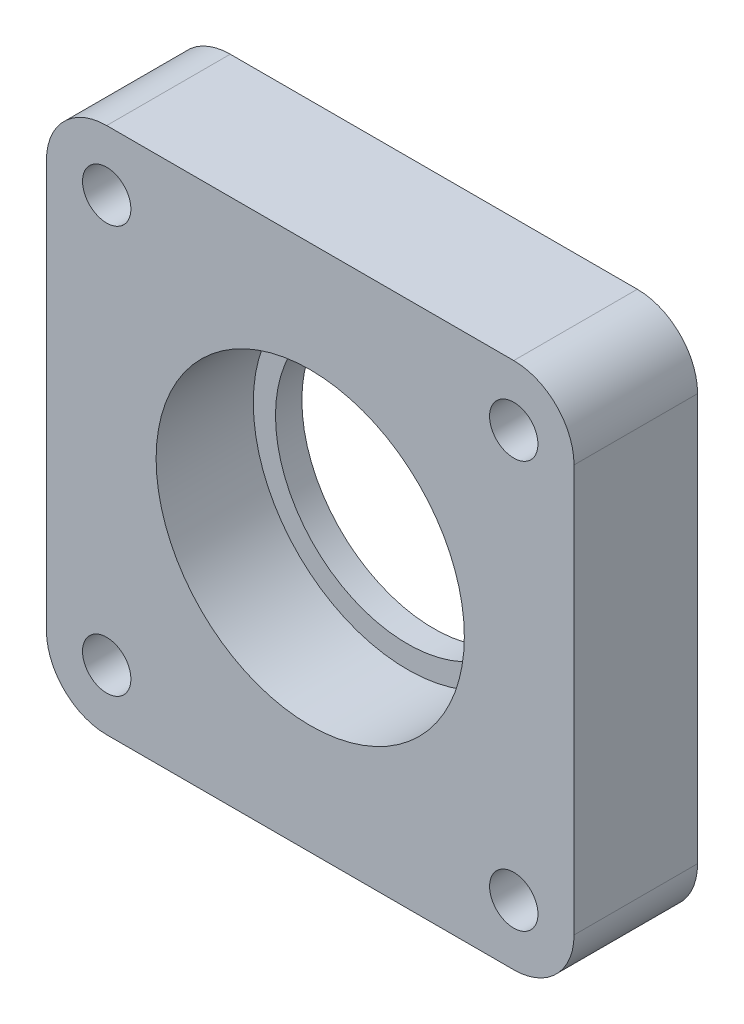
SolidWorks part; units mm, degrees
ref_plane "Alzado" through (0, 0, 0) normal (0, 0, 1) x (1, 0, 0)
ref_plane "Planta" through (0, 0, 0) normal (0, 1, 0) x (1, 0, 0)
ref_plane "Vista lateral" through (0, 0, 0) normal (1, 0, 0) x (0, 0, -1)
sketch "Croquis1" plane through (0, 0, 0) normal (0, 0, 1) x (1, 0, 0)
  line L0 (-122.1468, 83.6784) -> (-122.1468, -52.8591) construction
  line L5 (-172.2499, 0.9592) -> (-2.4287, 0.9592) construction
  line L7 (-99.0018, 30.9592) -> (-145.2918, 30.9592)
  line L8 (-92.1468, 24.1042) -> (-92.1468, -22.1858)
  line L13 (-99.0018, -29.0408) -> (-145.2918, -29.0408)
  line L14 (-152.1468, 24.1042) -> (-152.1468, -22.1858)
  line L15 (-92.1468, 30.9592) -> (-152.1468, -29.0408) construction
  line L16 (-92.1468, -29.0408) -> (-152.1468, 30.9592) construction
  circle A0 centre (-145.2918, 24.1042) radius 2.75
  circle A1 centre (-145.2918, -22.1858) radius 2.75
  circle A2 centre (-99.0018, -22.1858) radius 2.75
  circle A3 centre (-99.0018, 24.1042) radius 2.75
  circle A4 centre (-122.1468, 0.9592) radius 17.525
  arc A5 (-145.2918, 30.9592) -> (-152.1468, 24.1042) centre (-145.2918, 24.1042) ccw
  arc A6 (-145.2918, -29.0408) -> (-152.1468, -22.1858) centre (-145.2918, -22.1858) cw
  arc A7 (-99.0018, -29.0408) -> (-92.1468, -22.1858) centre (-99.0018, -22.1858) ccw
  arc A8 (-99.0018, 30.9592) -> (-92.1468, 24.1042) centre (-99.0018, 24.1042) cw
  dimension "D3" = 5.5
  dimension "D1" = 46.29
  dimension "D5" = 46.29
  dimension "D6" = 46.29
  dimension "D2" = 23.145
  dimension "D4" = 46.29
  dimension "D7" = 60
  dimension "D8" = 60
extrude "Saliente-Extruir1" add sketch "Croquis1" along normal blind 14.05
sketch "Croquis3" plane through (0, 0, 0) normal (0, 0, -1) x (-1, 0, 0)
  line L0 (122.1468, 18.4842) -> (122.1468, -16.5658) construction
  line L1 (104.6218, 0.9592) -> (139.6718, 0.9592) construction
  circle A0 centre (122.1468, 0.9592) radius 17.525 construction
  circle A1 centre (122.1468, 0.9592) radius 15
  circle A2 centre (122.1468, 0.9592) radius 20
extrude "Saliente-Extruir2" add sketch "Croquis3" against normal blind 3
